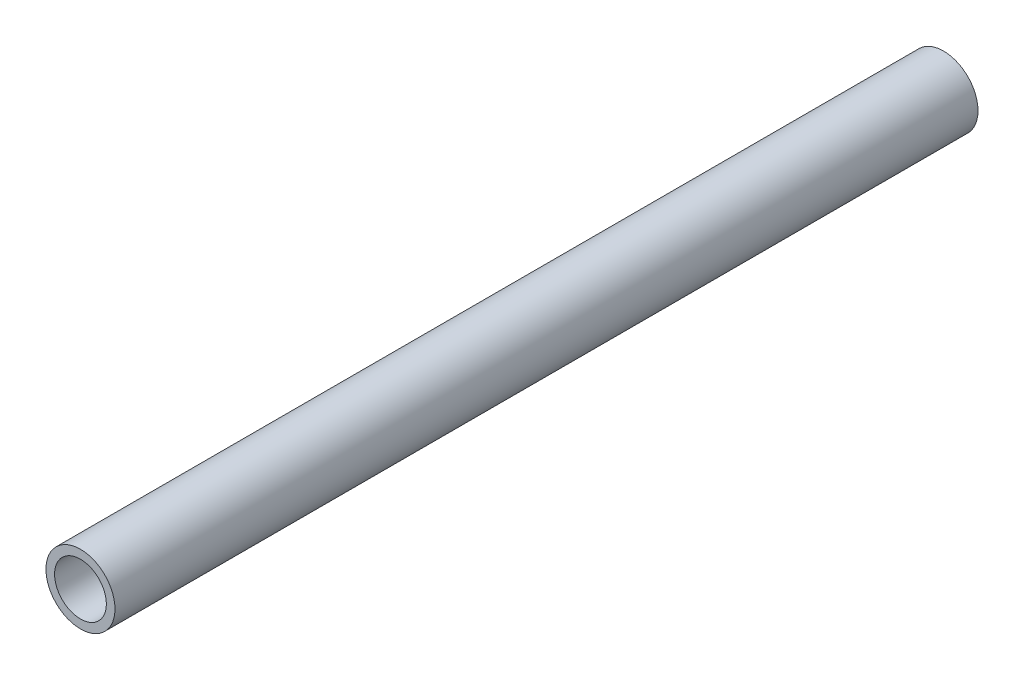
SolidWorks part; units mm, degrees
ref_plane "Front Plane" through (0, 0, 0) normal (0, 0, 1) x (1, 0, 0)
ref_plane "Top Plane" through (0, 0, 0) normal (0, 1, 0) x (1, 0, 0)
ref_plane "Right Plane" through (0, 0, 0) normal (1, 0, 0) x (0, 0, -1)
sketch "Sketch1" plane through (0, 0, 0) normal (0, 0, 1) x (1, 0, 0)
  circle A0 centre (0, 0) radius 4
  circle A1 centre (0, 0) radius 3
  dimension "D1" = 8
  dimension "D2" = 6
extrude "Boss-Extrude1" add sketch "Sketch1" along normal mid plane 100
sketch "Sketch2" plane through (0, 0, 0) normal (0, 0, 1) x (1, 0, 0)
  line L0 (0, 0) -> (0, 4) construction
  circle A0 centre (0, 0) radius 4 construction
